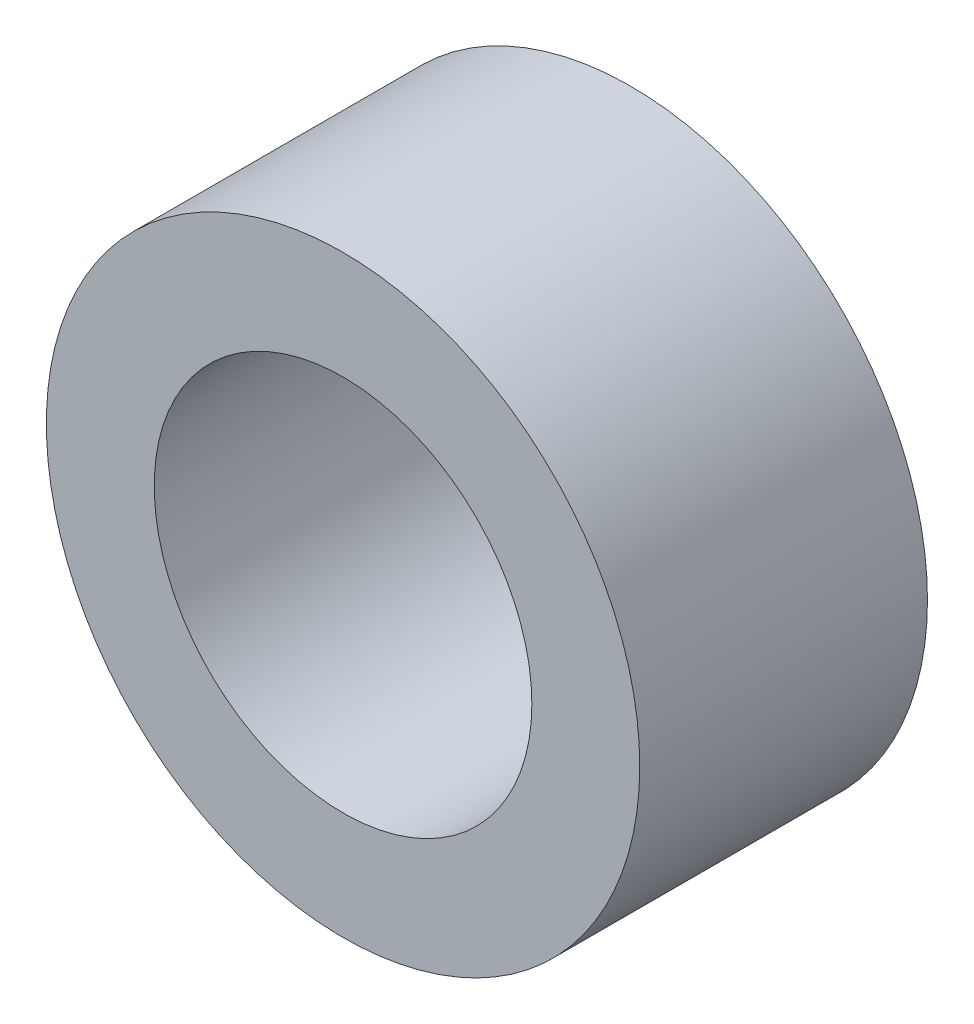
SolidWorks part; units mm, degrees
ref_plane "Front Plane" through (0, 0, 0) normal (0, 0, 1) x (1, 0, 0)
ref_plane "Top Plane" through (0, 0, 0) normal (0, 1, 0) x (1, 0, 0)
ref_plane "Right Plane" through (0, 0, 0) normal (1, 0, 0) x (0, 0, -1)
sketch "Sketch1" plane through (0, 0, 0) normal (0, 0, 1) x (1, 0, 0)
  circle A0 centre (0, 0) radius 5.25
  circle A1 centre (0, 0) radius 8.25
  dimension "D1" = 10.5
  dimension "D2" = 3
extrude "Boss-Extrude1" add sketch "Sketch1" along normal blind 8
